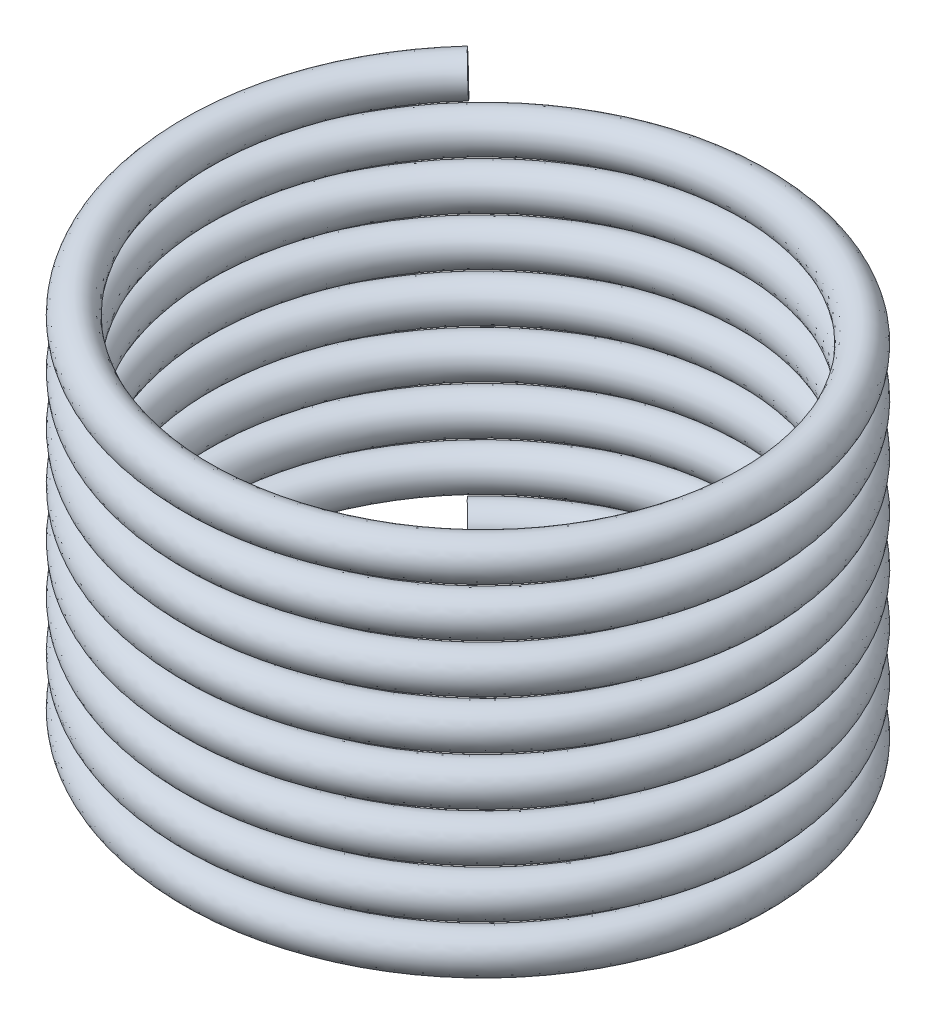
SolidWorks part; units mm, degrees
ref_plane "Ebene vorne" through (0, 0, 0) normal (0, 0, 1) x (1, 0, 0)
ref_plane "Ebene oben" through (0, 0, 0) normal (0, 1, 0) x (1, 0, 0)
ref_plane "Ebene rechts" through (0, 0, 0) normal (1, 0, 0) x (0, 0, -1)
sketch "Skizze1" plane through (0, 0, 0) normal (0, 1, 0) x (1, 0, 0)
  circle A0 centre (0, 0) radius 28.6223
curve "Spirale/Helix1" pitch 5 height 40 turns 8
sweep "Austragung2" add path "Spirale/Helix1" circular profile diameter 4 parameters "D3"=4
